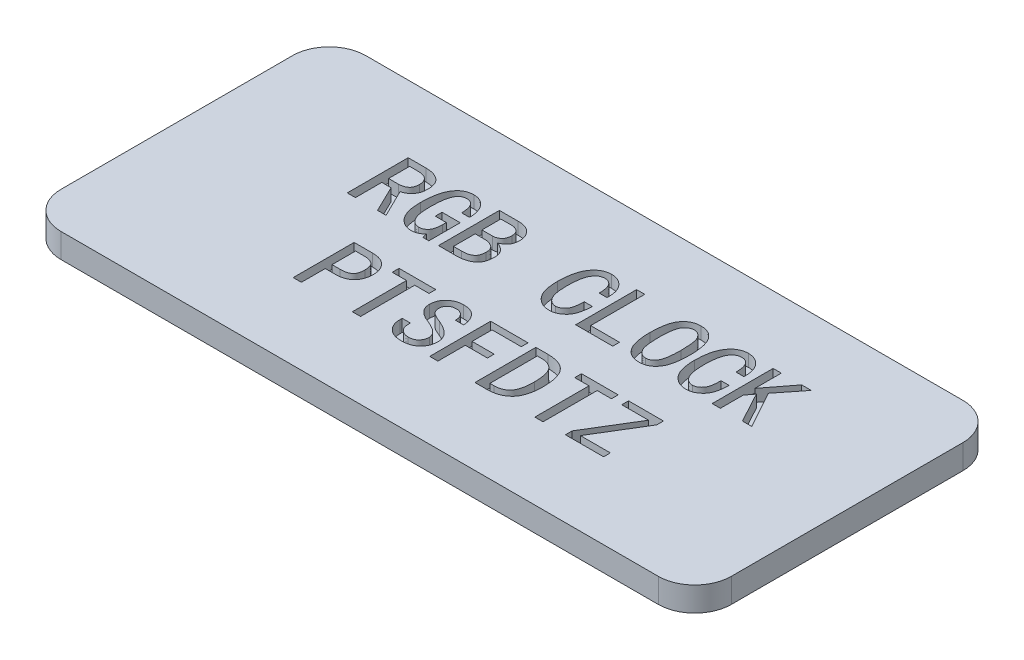
SolidWorks part; units mm, degrees
ref_plane "前视基准面" through (0, 0, 0) normal (0, 0, 1) x (1, 0, 0)
ref_plane "上视基准面" through (0, 0, 0) normal (0, 1, 0) x (1, 0, 0)
ref_plane "右视基准面" through (0, 0, 0) normal (1, 0, 0) x (0, 0, -1)
other "Configuration Table"
sketch "草图1" plane through (0, 0, 0) normal (0, 1, 0) x (1, 0, 0)
  line L0 (-49.0601, -24.953) -> (48.9399, -24.953)
  line L1 (-55.0601, -18.953) -> (-55.0601, 19.047)
  line L2 (-49.0601, 25.047) -> (48.9399, 25.047)
  line L3 (54.9399, -18.953) -> (54.9399, 19.047)
  line L4 (-55.0601, -24.953) -> (54.9399, 25.047) construction
  line L5 (-55.0601, 25.047) -> (54.9399, -24.953) construction
  arc A0 (48.9399, -24.953) -> (54.9399, -18.953) centre (48.9399, -18.953) ccw
  arc A1 (-55.0601, 19.047) -> (-49.0601, 25.047) centre (-49.0601, 19.047) cw
  arc A2 (-49.0601, -24.953) -> (-55.0601, -18.953) centre (-49.0601, -18.953) cw
  arc A3 (48.9399, 25.047) -> (54.9399, 19.047) centre (48.9399, 19.047) cw
  point P0 (-0.0601, 0.047)
  dimension "D2" = 6
  dimension "D1" = 50
extrude "凸台-拉伸1" add sketch "草图1" along normal blind 4
sketch "草图2" plane through (0, 4, 0) normal (0, 1, 0) x (1, 0, 0)
  text T0 "RGB CLOCK\r\n PTSFDTZ" font "黑体" height 10
extrude "切除-拉伸1" cut sketch "草图2" against normal blind 2
sketch "草图3" plane through (0, 0, 0) normal (0, -1, 0) x (1, 0, 0)
  line L0 (0, 0) -> (50000, 0) construction
  circle A0 centre (-0.0601, 22.653) radius 1.55
  circle A1 centre (19.9399, 22.653) radius 1.55
  circle A2 centre (39.9399, 22.653) radius 1.55
  circle A3 centre (-20.0601, 22.653) radius 1.55
  circle A4 centre (-40.0601, 22.653) radius 1.55
  circle A5 centre (-40.0601, -22.653) radius 1.55
  circle A6 centre (-20.0601, -22.653) radius 1.55
  circle A7 centre (39.9399, -22.653) radius 1.55
  circle A8 centre (19.9399, -22.653) radius 1.55
  circle A9 centre (-0.0601, -22.653) radius 1.55
  dimension "D1" = 3
  dimension "D2" = 3
extrude "切除-拉伸2" cut sketch "草图3" against normal blind 2
